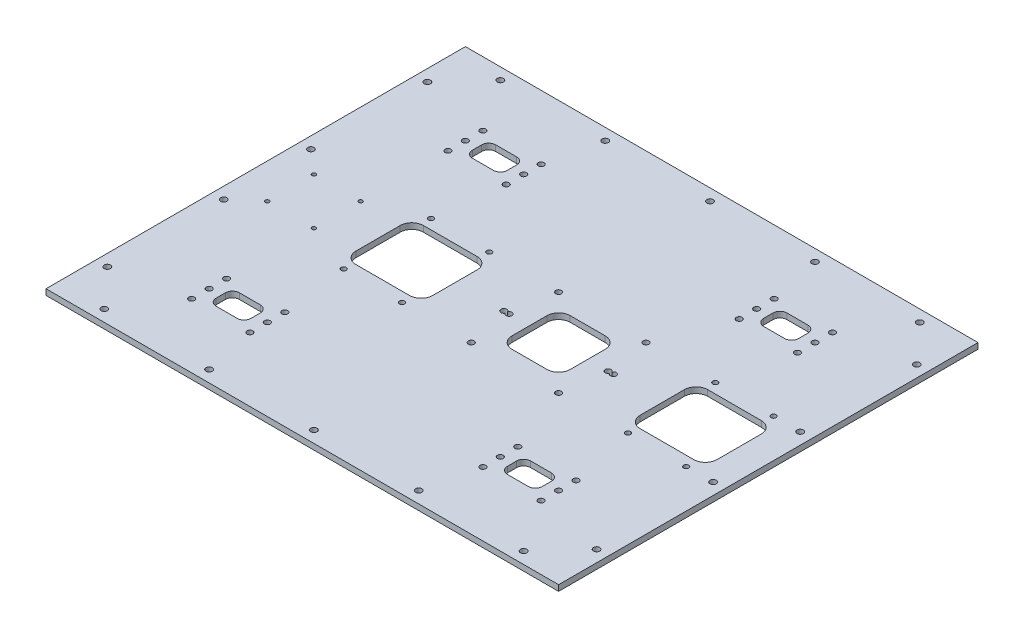
SolidWorks part; units mm, degrees
ref_plane "Plan de face" through (0, 0, 0) normal (0, 0, 1) x (1, 0, 0)
ref_plane "Plan de dessus" through (0, 0, 0) normal (0, 1, 0) x (1, 0, 0)
ref_plane "Plan de droite" through (0, 0, 0) normal (1, 0, 0) x (0, 0, -1)
sketch "Esquisse1" plane through (0, 0, 0) normal (0, 1, 0) x (1, 0, 0)
  line L0 (0, 180) -> (440, 180) construction
  line L1 (0, 0) -> (440, 0)
  line L2 (0, 0) -> (0, 360)
  line L3 (0, 360) -> (440, 360)
  line L4 (440, 0) -> (440, 360)
  line L5 (10, 350) -> (430, 350) construction
  line L6 (430, 10) -> (430, 350) construction
  line L7 (10, 10) -> (430, 10) construction
  line L8 (10, 10) -> (10, 350) construction
  line L9 (20, 340) -> (420, 340) construction
  line L10 (420, 20) -> (420, 340) construction
  line L11 (20, 20) -> (420, 20) construction
  line L12 (20, 20) -> (20, 340) construction
  line L16 (220, 360) -> (220, 0) construction
  circle A1 centre (40, 350) radius 2.7
  circle A2 centre (130, 350) radius 2.7
  circle A3 centre (220, 350) radius 2.7
  circle A4 centre (310, 350) radius 2.7
  circle A5 centre (400, 350) radius 2.7
  circle A6 centre (400, 10) radius 2.7
  circle A7 centre (310, 10) radius 2.7
  circle A8 centre (220, 10) radius 2.7
  circle A9 centre (130, 10) radius 2.7
  circle A10 centre (40, 10) radius 2.7
  circle A11 centre (10, 217.3673) radius 2.7
  circle A12 centre (10, 317.3673) radius 2.7
  circle A13 centre (10, 42.6327) radius 2.7
  circle A14 centre (10, 142.6327) radius 2.7
  circle A15 centre (430, 142.6327) radius 2.7
  circle A16 centre (430, 42.6327) radius 2.7
  circle A17 centre (430, 317.3673) radius 2.7
  circle A18 centre (430, 217.3673) radius 2.7
  dimension "D6" = 5.4
  dimension "D9" = 5.4
  dimension "D1" = 360
  dimension "D2" = 440
  dimension "D7" = 40
  dimension "D10" = 37.3673
  dimension "D3" = 10
  dimension "D4" = 10
  dimension "D8" = 5
  dimension "D11" = 2
extrude "Boss.-Extru.1" add sketch "Esquisse1" along normal blind 5
sketch "Esquisse2" plane through (0, 5, 0) normal (0, 1, 0) x (1, 0, 0)
  line L0 (0, 180) -> (440, 180) construction
  line L1 (0, 360) -> (0, 0) construction
  line L2 (440, 0) -> (440, 360) construction
  line L3 (50, 205) -> (50, 180) construction
  line L4 (75, 205) -> (25, 205) construction
  line L5 (75, 205) -> (75, 155) construction
  line L6 (75, 155) -> (25, 155) construction
  line L7 (25, 205) -> (25, 155) construction
  line L8 (75, 205) -> (25, 155) construction
  line L9 (75, 155) -> (25, 205) construction
  line L10 (260, 180) -> (260, 193.6034) construction
  line L11 (171, 209) -> (105, 209)
  line L12 (171, 209) -> (171, 151)
  line L13 (171, 151) -> (105, 151)
  line L14 (105, 209) -> (105, 151)
  line L15 (171, 209) -> (105, 151) construction
  line L16 (171, 151) -> (105, 209) construction
  line L17 (382, 180) -> (382, 151) construction
  line L18 (297.5, 217.5) -> (222.5, 217.5) construction
  line L19 (297.5, 217.5) -> (297.5, 142.5) construction
  line L20 (297.5, 142.5) -> (222.5, 142.5) construction
  line L21 (222.5, 217.5) -> (222.5, 142.5) construction
  line L22 (297.5, 217.5) -> (222.5, 142.5) construction
  line L23 (297.5, 142.5) -> (222.5, 217.5) construction
  line L24 (349, 209) -> (415, 209)
  line L25 (349, 209) -> (349, 151)
  line L26 (349, 151) -> (415, 151)
  line L27 (415, 209) -> (415, 151)
  line L28 (349, 209) -> (415, 151) construction
  line L29 (349, 151) -> (415, 209) construction
  line L30 (138, 180) -> (138, 151) construction
  line L32 (235, 205) -> (285, 205)
  line L33 (235, 205) -> (235, 155)
  line L34 (235, 155) -> (285, 155)
  line L35 (285, 205) -> (285, 155)
  line L36 (235, 205) -> (285, 155) construction
  line L37 (235, 155) -> (285, 205) construction
  circle A0 centre (30, 200) radius 1.7
  circle A1 centre (70, 200) radius 1.7
  circle A2 centre (70, 160) radius 1.7
  circle A3 centre (30, 160) radius 1.7
  arc A4 (215.25, 181.0897) -> (215.25, 178.9103) centre (213, 180) ccw
  arc A5 (304.75, 178.9103) -> (304.75, 181.0897) centre (307, 180) ccw
  arc A6 (215.25, 178.9103) -> (215.25, 181.0897) centre (217.5, 180) ccw
  arc A7 (304.75, 181.0897) -> (304.75, 178.9103) centre (302.5, 180) ccw
  circle A8 centre (222.5, 217.5) radius 2.5
  circle A9 centre (297.5, 217.5) radius 2.5
  circle A10 centre (222.5, 142.5) radius 2.5
  circle A11 centre (297.5, 142.5) radius 2.5
  circle A12 centre (407, 142.5) radius 2.2
  circle A13 centre (357, 142.5) radius 2.2
  circle A14 centre (357, 217.5) radius 2.2
  circle A15 centre (407, 217.5) radius 2.2
  circle A16 centre (163, 142.5) radius 2.2
  circle A17 centre (113, 142.5) radius 2.2
  circle A18 centre (113, 217.5) radius 2.2
  circle A19 centre (163, 217.5) radius 2.2
  point P6 (50, 180)
  point P21 (138, 180)
  point P44 (382, 180)
  dimension "D5" = 3.4
  dimension "D9" = 5
  dimension "D13" = 5
  dimension "D17" = 4.4
  dimension "D1" = 25
  dimension "D2" = 50
  dimension "D3" = 40
  dimension "D4" = 40
  dimension "D6" = 58
  dimension "D7" = 30
  dimension "D8" = 66
  dimension "D10" = 94
  dimension "D11" = 85
  dimension "D12" = 75
  dimension "D14" = 260
  dimension "D15" = 75
  dimension "D16" = 50
  dimension "D18" = 75
  dimension "D19" = 50
  dimension "D20" = 50
  dimension "D21" = 50
extrude "Enlèv. mat.-Extru.1" cut sketch "Esquisse2" against normal through all
fillet "Congé1" radius 10 12 edges at (171, 2.5, -209) (171, 2.5, -151) (105, 2.5, -151) (105, 2.5, -209) (415, 2.5, -151) (349, 2.5, -151) (349, 2.5, -209) (415, 2.5, -209) (235, 2.5, -155) (235, 2.5, -205) (285, 2.5, -205) (285, 2.5, -155)
sketch "Esquisse4" plane through (0, 5, 0) normal (0, 1, 0) x (1, 0, 0)
  line L0 (0, 180) -> (220, 180) construction
  line L1 (0, 360) -> (0, 0) construction
  line L2 (220, 180) -> (220, 360) construction
  line L3 (440, 360) -> (0, 360) construction
  line L4 (70, 290) -> (120, 290) construction
  line L5 (95, 300) -> (95, 290) construction
  line L6 (80, 300) -> (110, 300)
  line L7 (80, 300) -> (80, 280)
  line L8 (80, 280) -> (110, 280)
  line L9 (110, 300) -> (110, 280)
  line L10 (80, 300) -> (110, 280) construction
  line L11 (80, 280) -> (110, 300) construction
  line L12 (70, 290) -> (70, 305) construction
  line L13 (370, 290) -> (370, 305) construction
  line L14 (360, 280) -> (330, 300) construction
  line L15 (360, 300) -> (330, 280) construction
  line L16 (345, 300) -> (345, 290) construction
  line L17 (370, 290) -> (320, 290) construction
  line L18 (330, 300) -> (330, 280)
  line L19 (360, 280) -> (330, 280)
  line L20 (360, 300) -> (360, 280)
  line L21 (360, 300) -> (330, 300)
  line L22 (370, 70) -> (320, 70) construction
  line L23 (345, 60) -> (345, 70) construction
  line L24 (360, 60) -> (330, 80) construction
  line L25 (360, 80) -> (330, 60) construction
  line L26 (370, 70) -> (370, 55) construction
  line L27 (70, 70) -> (70, 55) construction
  line L28 (80, 80) -> (110, 60) construction
  line L29 (80, 60) -> (110, 80) construction
  line L30 (95, 60) -> (95, 70) construction
  line L31 (70, 70) -> (120, 70) construction
  line L32 (360, 60) -> (330, 60)
  line L33 (360, 60) -> (360, 80)
  line L34 (360, 80) -> (330, 80)
  line L35 (330, 60) -> (330, 80)
  line L36 (110, 60) -> (110, 80)
  line L37 (80, 80) -> (110, 80)
  line L38 (80, 60) -> (80, 80)
  line L39 (80, 60) -> (110, 60)
  circle A0 centre (70, 290) radius 2.5
  circle A1 centre (120, 290) radius 2.5
  circle A2 centre (70, 305) radius 2.5
  circle A3 centre (70, 275) radius 2.5
  circle A4 centre (120, 275) radius 2.5
  circle A5 centre (120, 305) radius 2.5
  circle A6 centre (320, 305) radius 2.5
  circle A7 centre (320, 275) radius 2.5
  circle A8 centre (370, 275) radius 2.5
  circle A9 centre (370, 305) radius 2.5
  circle A10 centre (320, 290) radius 2.5
  circle A11 centre (370, 290) radius 2.5
  circle A12 centre (370, 70) radius 2.5
  circle A13 centre (320, 70) radius 2.5
  circle A14 centre (370, 55) radius 2.5
  circle A15 centre (370, 85) radius 2.5
  circle A16 centre (320, 85) radius 2.5
  circle A17 centre (320, 55) radius 2.5
  circle A18 centre (120, 55) radius 2.5
  circle A19 centre (120, 85) radius 2.5
  circle A20 centre (70, 85) radius 2.5
  circle A21 centre (70, 55) radius 2.5
  circle A22 centre (120, 70) radius 2.5
  circle A23 centre (70, 70) radius 2.5
  point P12 (95, 290)
  point P45 (345, 290)
  point P82 (345, 70)
  point P83 (95, 70)
  dimension "D1" = 5
  dimension "D2" = 50
  dimension "D3" = 30
  dimension "D4" = 20
  dimension "D5" = 30
  dimension "D6" = 250
  dimension "D7" = 220
extrude "Enlèv. mat.-Extru.2" cut sketch "Esquisse4" against normal blind 10
fillet "Congé2" radius 6 16 edges at (110, 2.5, -280) (80, 2.5, -280) (80, 2.5, -300) (110, 2.5, -300) (80, 2.5, -80) (110, 2.5, -60) (80, 2.5, -60) (110, 2.5, -80) (360, 2.5, -60) (330, 2.5, -60) (330, 2.5, -80) (360, 2.5, -80) (360, 2.5, -280) (330, 2.5, -280) (330, 2.5, -300) (360, 2.5, -300)
